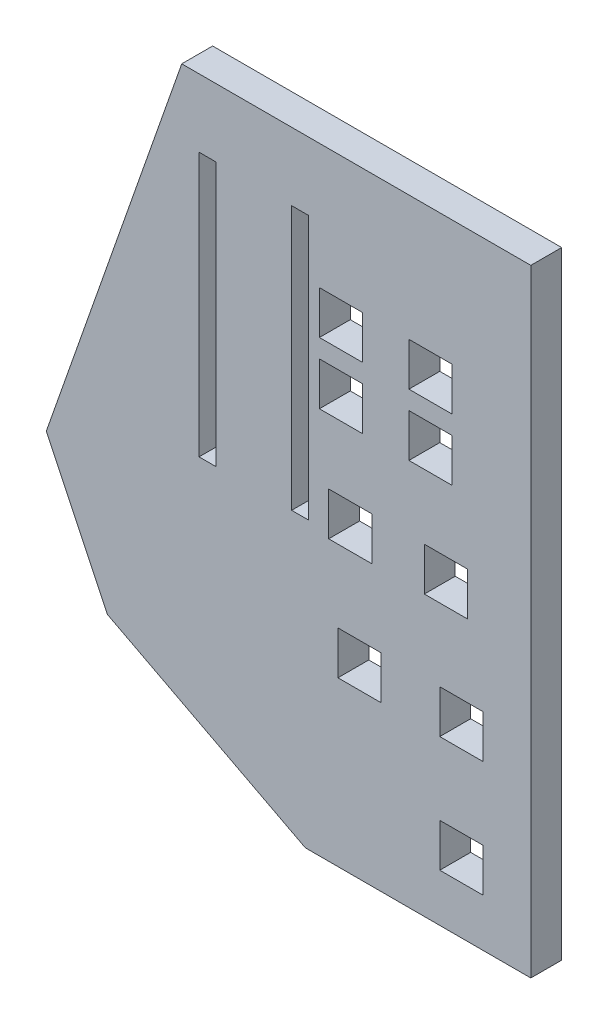
SolidWorks part; units mm, degrees
ref_plane "Front Plane" through (0, 0, 0) normal (0, 0, 1) x (1, 0, 0)
ref_plane "Top Plane" through (0, 0, 0) normal (0, 1, 0) x (1, 0, 0)
ref_plane "Right Plane" through (0, 0, 0) normal (1, 0, 0) x (0, 0, -1)
sketch "Sketch1" plane through (0, 0, 0) normal (0, 0, 1) x (1, 0, 0)
  line L6 (-20.066, -57.15) -> (46.99, -57.15) construction
  line L7 (-12.446, -73.152) -> (46.99, -73.152) construction
  line L8 (-4.1204, 6.35) -> (53.34, 6.35)
  line L9 (53.34, 6.35) -> (53.34, -95.25)
  line L10 (53.34, -95.25) -> (16.225, -95.25)
  line L16 (-4.1204, 6.35) -> (-26.416, -57.15)
  line L18 (-20.066, -57.15) -> (-26.416, -57.15) construction
  line L26 (0, 0) -> (46.99, 0) construction
  line L27 (46.99, 0) -> (46.99, -88.9) construction
  line L28 (46.99, -88.9) -> (17.78, -88.9) construction
  line L29 (17.78, -88.9) -> (-12.446, -73.152) construction
  line L30 (-12.446, -73.152) -> (-20.066, -57.15) construction
  line L31 (-20.066, -57.15) -> (0, 0) construction
  line L32 (46.99, -57.15) -> (46.99, -88.9) construction
  line L33 (17.78, -88.9) -> (16.225, -95.25) construction
  line L34 (-12.446, -73.152) -> (-17.9301, -78.4424) construction
  line L35 (16.225, -95.25) -> (-16.3566, -78.2747)
  line L36 (-26.416, -57.15) -> (-16.3566, -78.2747)
  point P40 (24.6098, 6.35)
  dimension "D1" = 88.9
  dimension "D2" = 29.21
  dimension "D3" = 59.436
  dimension "D4" = 67.056
  dimension "D5" = 6.35
  dimension "D6" = 6.35
  dimension "D7" = 46.99
  dimension "D8" = 6.35
  dimension "D13" = 103.76
  dimension "D14" = 6.35
  dimension "D17" = 108.51
  dimension "D22" = 5.7332
extrude "Boss-Extrude1" add sketch "Sketch1" along normal blind 5.08
sketch "Sketch3" plane through (0, 0, 5.08) normal (0, 0, 1) x (1, 0, 0)
  line L0 (46.99, -88.9) -> (0, -88.9) construction
  line L6 (-20.066, -57.15) -> (46.99, -57.15) construction
  line L7 (-12.446, -73.152) -> (46.99, -73.152) construction
  line L8 (0, 0) -> (46.99, 0) construction
  line L9 (46.99, 0) -> (46.99, -88.9) construction
  line L10 (46.99, -88.9) -> (17.78, -88.9) construction
  line L11 (17.78, -88.9) -> (-12.446, -73.152) construction
  line L12 (-12.446, -73.152) -> (-20.066, -57.15) construction
  line L13 (-20.066, -57.15) -> (0, 0) construction
sketch "Sketch5" plane through (0, 0, 0) normal (0, 0, -1) x (-1, 0, 0)
  line L0 (-46.99, 0) -> (-46.99, -17.78) construction
  line L1 (-46.99, 0) -> (-1.524, 0) construction
  line L2 (-46.99, -17.78) -> (-36.83, -17.78) construction
  line L3 (-46.99, 0) -> (-46.99, -27.94) construction
  line L8 (-40.386, -14.224) -> (-33.274, -14.224)
  line L9 (-40.386, -14.224) -> (-40.386, -21.336)
  line L10 (-46.99, 0) -> (-46.99, -45.72) construction
  line L15 (-40.386, -21.336) -> (-33.274, -21.336)
  line L16 (-33.274, -14.224) -> (-33.274, -21.336)
  line L17 (-46.99, 0) -> (-46.99, -88.9) construction
  line L18 (-46.99, -45.72) -> (-39.37, -45.72) construction
  line L19 (-40.386, -14.224) -> (-33.274, -21.336) construction
  line L20 (-46.99, 0) -> (-46.99, -64.77) construction
  line L21 (-42.926, -42.164) -> (-35.814, -42.164)
  line L22 (-42.926, -42.164) -> (-42.926, -49.276)
  line L23 (-42.926, -49.276) -> (-35.814, -49.276)
  line L24 (-35.814, -42.164) -> (-35.814, -49.276)
  line L25 (-42.926, -42.164) -> (-35.814, -49.276) construction
  line L26 (-42.926, -49.276) -> (-35.814, -42.164) construction
  line L27 (-46.99, -64.77) -> (-41.91, -64.77) construction
  line L28 (-40.386, -21.336) -> (-33.274, -14.224) construction
  line L29 (-46.99, -27.94) -> (-36.83, -27.94) construction
  line L30 (-46.99, 0) -> (-46.99, -83.82) construction
  line L31 (-40.386, -24.384) -> (-33.274, -24.384)
  line L32 (-40.386, -24.384) -> (-40.386, -31.496)
  line L33 (-40.386, -31.496) -> (-33.274, -31.496)
  line L34 (-33.274, -24.384) -> (-33.274, -31.496)
  line L35 (-40.386, -24.384) -> (-33.274, -31.496) construction
  line L36 (-40.386, -31.496) -> (-33.274, -24.384) construction
  line L37 (-45.466, -61.214) -> (-38.354, -61.214)
  line L38 (-45.466, -61.214) -> (-45.466, -68.326)
  line L39 (-45.466, -68.326) -> (-38.354, -68.326)
  line L40 (-38.354, -61.214) -> (-38.354, -68.326)
  line L41 (-45.466, -61.214) -> (-38.354, -68.326) construction
  line L42 (-45.466, -68.326) -> (-38.354, -61.214) construction
  line L43 (-46.99, -83.82) -> (-41.91, -83.82) construction
  line L44 (-36.83, -17.78) -> (-22.098, -17.78) construction
  line L45 (-45.466, -80.264) -> (-38.354, -80.264)
  line L46 (-45.466, -80.264) -> (-45.466, -87.376)
  line L47 (-45.466, -87.376) -> (-38.354, -87.376)
  line L48 (-38.354, -80.264) -> (-38.354, -87.376)
  line L49 (-45.466, -80.264) -> (-38.354, -87.376) construction
  line L50 (-45.466, -87.376) -> (-38.354, -80.264) construction
  line L51 (-36.83, -27.94) -> (-22.098, -27.94) construction
  line L52 (-39.37, -45.72) -> (-23.622, -45.72) construction
  line L53 (-41.91, -64.77) -> (-25.146, -64.77) construction
  line L54 (-46.99, 0) -> (-16.764, 0) construction
  line L55 (-25.654, -14.224) -> (-18.542, -14.224)
  line L56 (-25.654, -14.224) -> (-25.654, -21.336)
  line L57 (-25.654, -21.336) -> (-18.542, -21.336)
  line L58 (-18.542, -14.224) -> (-18.542, -21.336)
  line L59 (-25.654, -14.224) -> (-18.542, -21.336) construction
  line L60 (-25.654, -21.336) -> (-18.542, -14.224) construction
  line L61 (-25.654, -24.384) -> (-18.542, -24.384)
  line L62 (-25.654, -24.384) -> (-25.654, -31.496)
  line L63 (-25.654, -31.496) -> (-18.542, -31.496)
  line L64 (-18.542, -24.384) -> (-18.542, -31.496)
  line L65 (-25.654, -24.384) -> (-18.542, -31.496) construction
  line L66 (-25.654, -31.496) -> (-18.542, -24.384) construction
  line L67 (-27.178, -42.164) -> (-20.066, -42.164)
  line L68 (-27.178, -42.164) -> (-27.178, -49.276)
  line L69 (-27.178, -49.276) -> (-20.066, -49.276)
  line L70 (-20.066, -42.164) -> (-20.066, -49.276)
  line L71 (-27.178, -42.164) -> (-20.066, -49.276) construction
  line L72 (-27.178, -49.276) -> (-20.066, -42.164) construction
  line L73 (-28.702, -61.214) -> (-21.59, -61.214)
  line L74 (-28.702, -61.214) -> (-28.702, -68.326)
  line L75 (-28.702, -68.326) -> (-21.59, -68.326)
  line L76 (-21.59, -61.214) -> (-21.59, -68.326)
  line L77 (-28.702, -61.214) -> (-21.59, -68.326) construction
  line L78 (-28.702, -68.326) -> (-21.59, -61.214) construction
  line L79 (0, 0) -> (-46.99, 0) construction
  line L80 (-16.764, 0) -> (-16.764, -4.826) construction
  line L81 (-46.99, 0) -> (-13.97, 0) construction
  line L82 (-13.97, 0) -> (-13.97, -4.826) construction
  line L83 (-1.524, 0) -> (-1.524, -4.826) construction
  line L84 (-46.99, 0) -> (-17.1256, 0) construction
  line L85 (-1.524, 0) -> (-1.524, -48.26) construction
  line L86 (-46.99, 0) -> (1.27, 0) construction
  line L87 (1.27, 0) -> (1.27, -4.826) construction
  line L88 (-16.764, 0) -> (-16.764, -48.26) construction
  line L90 (-16.764, -4.826) -> (-13.97, -4.826)
  line L91 (-16.764, -4.826) -> (-16.764, -48.26)
  line L92 (-16.764, -48.26) -> (-13.97, -48.26)
  line L93 (-13.97, -4.826) -> (-13.97, -48.26)
  line L94 (-1.524, -4.826) -> (1.27, -4.826)
  line L95 (-1.524, -4.826) -> (-1.524, -48.26)
  line L96 (-1.524, -48.26) -> (1.27, -48.26)
  line L97 (1.27, -4.826) -> (1.27, -48.26)
  dimension "D2" = 7.112
  dimension "D3" = 64.77
  dimension "D4" = 7.112
  dimension "D5" = 10.16
  dimension "D6" = 17.78
  dimension "D7" = 7.112
  dimension "D8" = 7.112
  dimension "D9" = 45.72
  dimension "D10" = 7.62
  dimension "D11" = 7.112
  dimension "D12" = 7.112
  dimension "D13" = 27.94
  dimension "D14" = 10.16
  dimension "D15" = 5.08
  dimension "D16" = 7.112
  dimension "D17" = 7.112
  dimension "D18" = 7.112
  dimension "D19" = 7.112
  dimension "D20" = 83.82
  dimension "D21" = 5.08
  dimension "D22" = 7.112
  dimension "D23" = 7.112
  dimension "D24" = 14.732
  dimension "D25" = 7.112
  dimension "D26" = 7.112
  dimension "D27" = 14.732
  dimension "D28" = 7.112
  dimension "D29" = 7.112
  dimension "D30" = 15.748
  dimension "D31" = 7.112
  dimension "D32" = 7.112
  dimension "D33" = 16.764
  dimension "D34" = 30.226
  dimension "D35" = 4.826
  dimension "D36" = 33.02
  dimension "D37" = 4.826
  dimension "D38" = 45.466
  dimension "D39" = 4.826
  dimension "D40" = 48.26
  dimension "D41" = 4.826
  dimension "D42" = 48.26
  dimension "D43" = 48.26
extrude "Cut-Extrude1" cut sketch "Sketch5" against normal through all
